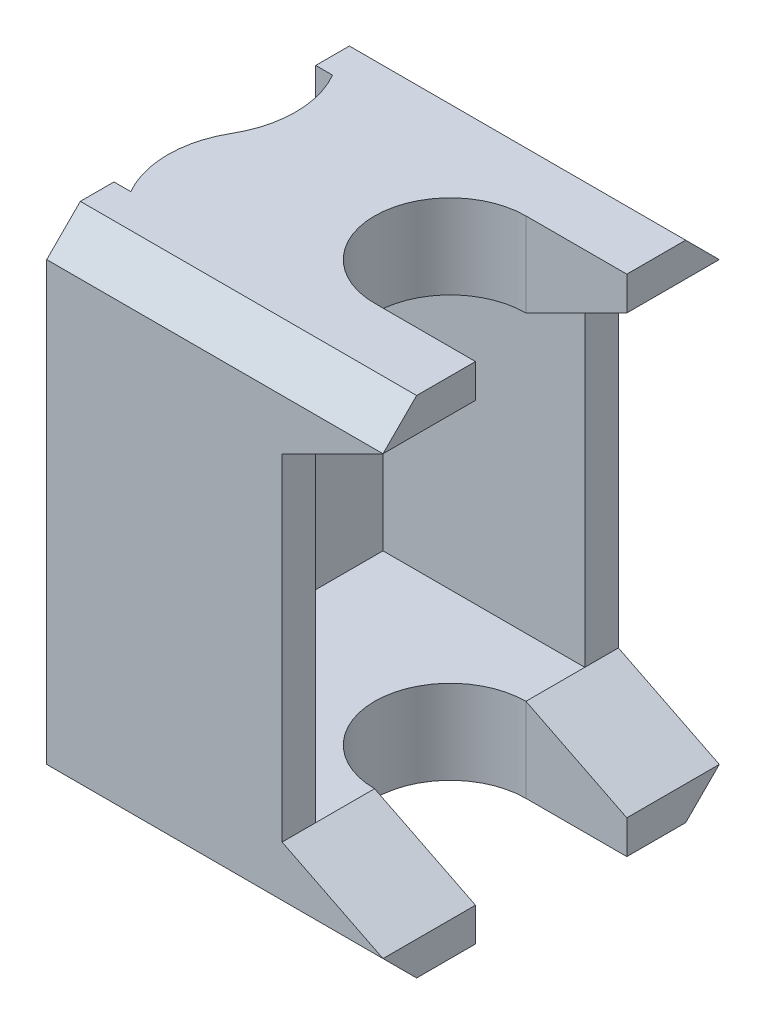
SolidWorks part; units mm, degrees
material "Plain Carbon Steel"
ref_plane "Front Plane" through (0, 0, 0) normal (0, 0, 1) x (1, 0, 0)
ref_plane "Top Plane" through (0, 0, 0) normal (0, 1, 0) x (1, 0, 0)
ref_plane "Right Plane" through (0, 0, 0) normal (1, 0, 0) x (0, 0, -1)
sketch "Sketch1" plane through (0, 0, 0) normal (0, 0, 1) x (1, 0, 0)
  line L0 (0, 0) -> (0, 10)
  line L1 (0, 10) -> (-30, 25)
  line L2 (-30, 25) -> (-30, 125)
  line L3 (-30, 125) -> (0, 140)
  line L4 (0, 140) -> (0, 150)
  line L5 (0, 150) -> (-100, 150)
  line L6 (-100, 150) -> (-100, 0)
  line L7 (-100, 0) -> (0, 0)
  point P9 (-30, 26.8215)
  dimension "D1" = 100
  dimension "D2" = 10
  dimension "D3" = 10
  dimension "D4" = 70
  dimension "D5" = 150
  dimension "D6" = 100
  dimension "D7" = 25
extrude "Boss-Extrude1" add sketch "Sketch1" along normal mid plane 100
sketch "Sketch2" plane through (0, 150, 0) normal (0, 1, 0) x (1, 0, 0)
  line L0 (0, 22.5) -> (-30, 22.5)
  line L1 (0, -50) -> (0, 50) construction
  line L2 (0, -22.5) -> (-30, -22.5)
  line L3 (0, -22.5) -> (0, 22.5)
  line L4 (-100, -30) -> (-95, -30)
  line L5 (-100, -50) -> (-100, 50) construction
  line L6 (-95, 30) -> (-100, 30)
  line L7 (-100, 30) -> (-100, -30)
  arc A0 (-30, -22.5) -> (-30, 22.5) centre (-30, 0) cw
  arc A1 (-95, -30) -> (-95, 0) centre (-69.0192, -15) cw
  arc A2 (-95, 0) -> (-95, 30) centre (-120.9808, 15) ccw
  point P17 (-100, 0)
  point P18 (-92.1757, 0)
  dimension "D4" = 30
  dimension "D5" = 30
  dimension "D1" = 45
  dimension "D2" = 30
  dimension "D3" = 60
  dimension "D6" = 5
  dimension "D7" = 5
extrude "Cut-Extrude1" cut sketch "Sketch2" against normal through all contours L3 L0 A0 L2 | L7 L4 A1 A2 L6
sketch "Sketch3" plane through (-30, 0, 0) normal (1, 0, 0) x (0, 0, -1)
  line L0 (-50, 25) -> (-22.5, 25) construction
  line L1 (-40, 25) -> (40, 25)
  line L2 (-40, 25) -> (-40, 125)
  line L3 (-40, 125) -> (40, 125)
  line L4 (40, 25) -> (40, 125)
  line L5 (22.5, 125) -> (50, 125) construction
  line L6 (-50, 25) -> (-50, 125) construction
  line L7 (50, 25) -> (50, 125) construction
  dimension "D1" = 10
  dimension "D2" = 10
extrude "Cut-Extrude3" cut sketch "Sketch3" against normal blind 60
sketch "Sketch4" plane through (0, 0, 0) normal (1, 0, 0) x (0, 0, -1)
  line L0 (-50, 140) -> (-40, 150)
  line L1 (-50, 150) -> (-22.5, 150) construction
  line L2 (-40, 150) -> (-50, 150)
  line L3 (-50, 140) -> (-50, 150)
  line L4 (50, 140) -> (50, 150)
  line L5 (50, 150) -> (40, 150)
  line L6 (22.5, 150) -> (50, 150) construction
  line L7 (40, 150) -> (50, 140)
  line L8 (-50, 10) -> (-50, 0)
  line L9 (-50, 0) -> (-40, 0)
  line L10 (-50, 0) -> (-22.5, 0) construction
  line L11 (-40, 0) -> (-50, 10)
  line L12 (40, 0) -> (50, 0)
  line L13 (22.5, 0) -> (50, 0) construction
  line L14 (50, 0) -> (50, 10)
  line L15 (50, 10) -> (40, 0)
  dimension "D1" = 45
  dimension "D2" = 45
  dimension "D3" = 45
  dimension "D4" = 45
extrude "Cut-Extrude4" cut sketch "Sketch4" against normal through all
